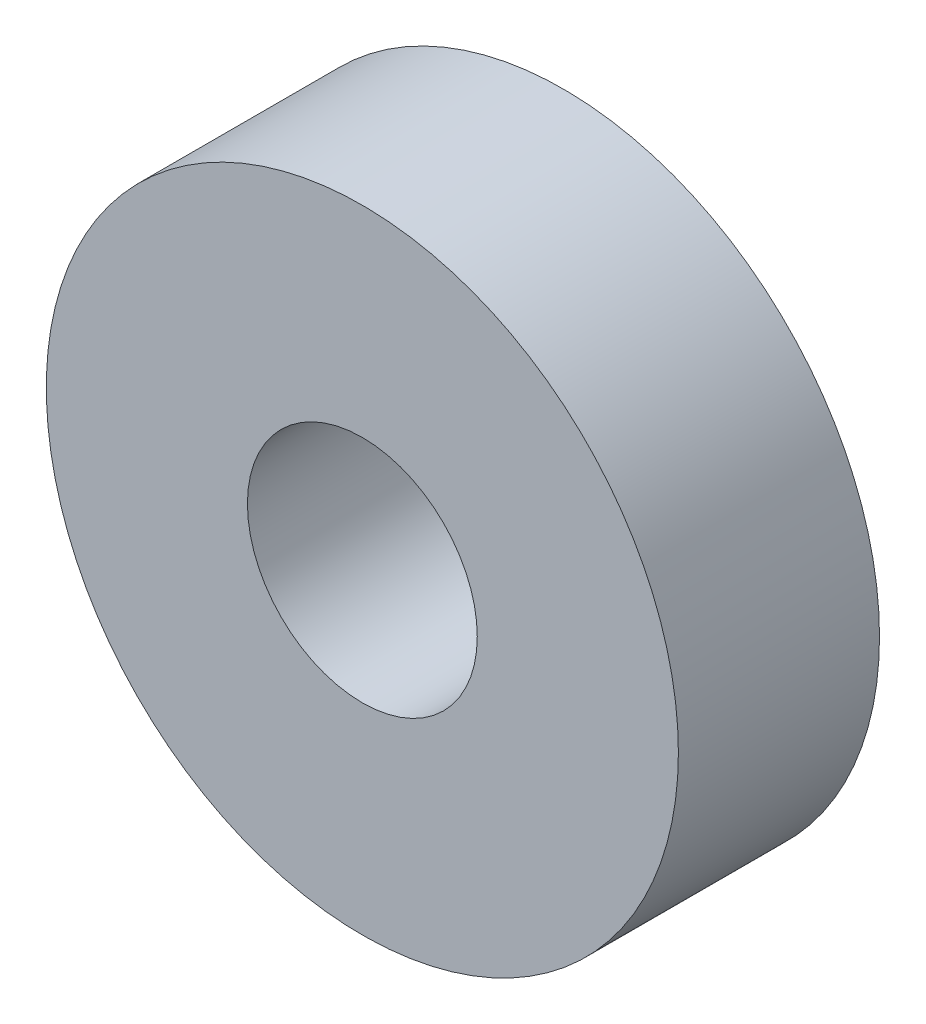
SolidWorks part; units mm, degrees
ref_plane "Front Plane" through (0, 0, 0) normal (0, 0, 1) x (1, 0, 0)
ref_plane "Top Plane" through (0, 0, 0) normal (0, 1, 0) x (1, 0, 0)
ref_plane "Right Plane" through (0, 0, 0) normal (1, 0, 0) x (0, 0, -1)
sketch "Sketch1" plane through (0, 0, 0) normal (0, 0, 1) x (1, 0, 0)
  circle A0 centre (0, 0) radius 11
  circle A1 centre (0, 0) radius 4
  dimension "D1" = 8
  dimension "D2" = 22
extrude "Boss-Extrude1" add sketch "Sketch1" along normal blind 7
